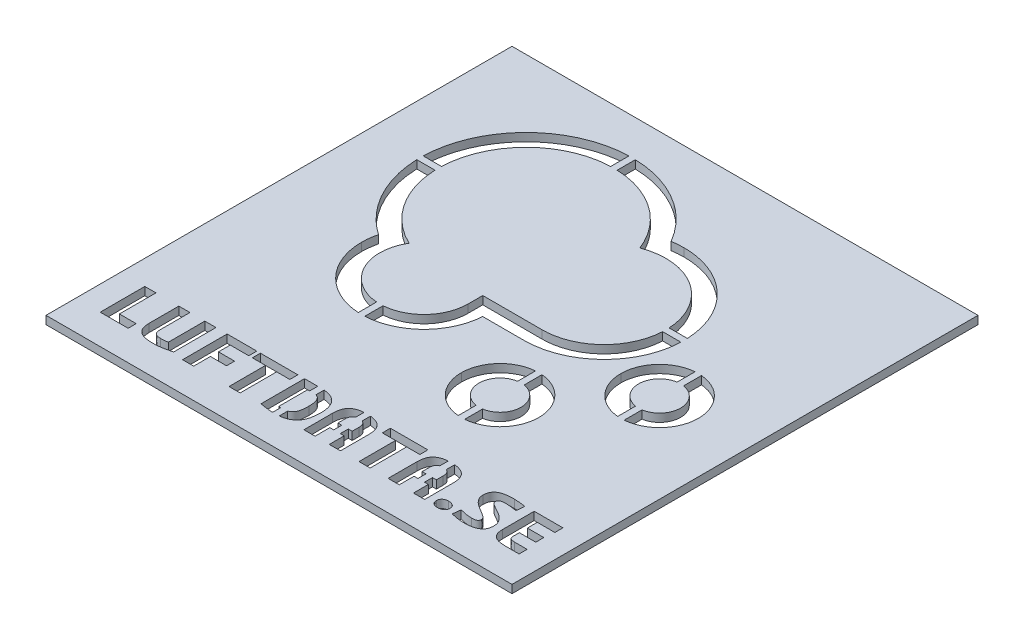
SolidWorks part; units mm, degrees
ref_plane "Front Plane" through (0, 0, 0) normal (0, 0, 1) x (1, 0, 0)
ref_plane "Top Plane" through (0, 0, 0) normal (0, 1, 0) x (1, 0, 0)
ref_plane "Right Plane" through (0, 0, 0) normal (1, 0, 0) x (0, 0, -1)
sketch "Logo" plane through (0, 0, 0) normal (0, 1, 0) x (1, 0, 0)
  line L0 (6.8222, -9.5648) -> (-7.8428, -9.5648)
  line L1 (-7.8428, -9.5648) -> (-7.8428, -13.1554)
  line L2 (-3.3693, -14.065) -> (6.822, -14.0654)
  line L4 (-45.0278, 38.3096) -> (45.0278, 38.3096) construction
  line L5 (-45.0278, 38.3096) -> (-45.0278, -38.3096) construction
  line L6 (-45.0278, -38.3096) -> (45.0278, -38.3096) construction
  line L7 (45.0278, 38.3096) -> (45.0278, -38.3096) construction
  spline S0 degree 3 poles (-18.8378, 33.8102) (-9.6328, 33.8102) (-1.7677, 28.0702) (1.3772, 19.9802) knots 0 0 0 0 1 1 1 1
  spline S1 degree 3 poles (1.3772, 19.9802) (3.0672, 20.6252) (4.9022, 20.9802) (6.8222, 20.9802) knots 1 1 1 1 2 2 2 2
  spline S2 degree 3 poles (6.8222, 20.9802) (15.2572, 20.9802) (22.0922, 14.1452) (22.0922, 5.7102) knots 2 2 2 2 3 3 3 3
  spline S3 degree 3 poles (22.0922, 5.7102) (22.0922, -2.7248) (15.2572, -9.5648) (6.8222, -9.5648) knots 3 3 3 3 4 4 4 4
  spline S4 degree 3 poles (-7.8428, -13.1554) (-7.8429, -19.1854) (-12.7331, -24.0753) (-18.7631, -24.0751) knots 6 6 6 6 7 7 7 7
  spline S5 degree 3 poles (-18.7631, -24.0751) (-24.7931, -24.0749) (-29.6829, -19.1848) (-29.6828, -13.1548) knots 7 7 7 7 8 8 8 8
  spline S6 degree 3 poles (-29.6828, -13.1548) (-29.6828, -11.0798) (-29.1028, -9.1398) (-28.0978, -7.4898) knots 8 8 8 8 9 9 9 9
  spline S7 degree 3 poles (-28.0978, -7.4898) (-35.4478, -4.0198) (-40.5278, 3.4602) (-40.5278, 12.1252) knots 9 9 9 9 10 10 10 10
  spline S8 degree 3 poles (-40.5278, 12.1252) (-40.5278, 24.1002) (-30.8178, 33.8102) (-18.8378, 33.8102) knots 10 10 10 10 11 11 11 11
  spline S9 degree 3 poles (-18.8378, 38.3096) (-33.279, 38.3096) (-45.0278, 26.5631) (-45.0278, 12.1246) knots 0 0 0 0 1 1 1 1
  spline S10 degree 3 poles (-45.0278, 12.1246) (-45.0278, 3.4834) (-40.7005, -4.5805) (-33.7243, -9.4193) knots 1 1 1 1 2 2 2 2
  spline S11 degree 3 poles (-33.7243, -9.4193) (-34.0275, -10.6346) (-34.1828, -11.8887) (-34.1828, -13.1554) knots 2 2 2 2 3 3 3 3
  spline S12 degree 3 poles (-34.1828, -13.1554) (-34.1828, -21.658) (-27.2654, -28.5754) (-18.7628, -28.5754) knots 3 3 3 3 4 4 4 4
  spline S13 degree 3 poles (-18.7628, -28.5754) (-10.5653, -28.5754) (-3.8414, -22.1461) (-3.3693, -14.065) knots 4 4 4 4 5 5 5 5
  spline S14 degree 3 poles (6.822, -14.0654) (17.7234, -14.0654) (26.5922, -5.1944) (26.5922, 5.7096) knots 6 6 6 6 7 7 7 7
  spline S15 degree 3 poles (26.5922, 5.7096) (26.5922, 16.6108) (17.7234, 25.4796) (6.8222, 25.4796) knots 7 7 7 7 8 8 8 8
  spline S16 degree 3 poles (6.8222, 25.4796) (5.8114, 25.4796) (4.8099, 25.4039) (3.8223, 25.2532) knots 8 8 8 8 9 9 9 9
  spline S17 degree 3 poles (3.8223, 25.2532) (1.9103, 28.5555) (-0.7065, 31.4051) (-3.8848, 33.6202) knots 9 9 9 9 10 10 10 10
  spline S18 degree 3 poles (-3.8848, 33.6202) (-8.2867, 36.688) (-13.4573, 38.3096) (-18.8378, 38.3096) knots 10 10 10 10 11 11 11 11
  spline S19 degree 3 poles (35.4472, -14.399) (32.584, -14.399) (30.2628, -12.0779) (30.2628, -9.2146) (30.2628, -6.3513) (32.584, -4.0302) (35.4472, -4.0302) knots 2 2 2 2 3 3 3 4 4 4 4
  spline S20 degree 3 poles (35.4472, -4.0302) (38.3105, -4.0302) (40.6316, -6.3513) (40.6316, -9.2146) (40.6316, -12.0779) (38.3105, -14.399) (35.4472, -14.399) knots 0 0 0 0 1 1 1 2 2 2 2
  spline S21 degree 3 poles (35.4472, 0.3545) (30.1708, 0.3545) (25.8782, -3.9382) (25.8782, -9.2146) knots 0 0 0 0 1 1 1 1
  spline S22 degree 3 poles (25.8782, -9.2146) (25.8782, -14.491) (30.1708, -18.7837) (35.4472, -18.7837) knots 1 1 1 1 2 2 2 2
  spline S23 degree 3 poles (35.4472, -18.7837) (40.7236, -18.7837) (45.0163, -14.491) (45.0163, -9.2146) knots 2 2 2 2 3 3 3 3
  spline S24 degree 3 poles (45.0163, -9.2146) (45.0163, -3.9382) (40.7236, 0.3545) (35.4472, 0.3545) knots 3 3 3 3 4 4 4 4
  spline S25 degree 3 poles (15.5836, -33.9035) (12.7203, -33.9035) (10.3992, -31.5824) (10.3992, -28.7191) (10.3992, -25.8559) (12.7203, -23.5347) (15.5836, -23.5347) knots 2 2 2 2 3 3 3 4 4 4 4
  spline S26 degree 3 poles (15.5836, -23.5347) (18.4468, -23.5347) (20.768, -25.8559) (20.768, -28.7191) (20.768, -31.5824) (18.4468, -33.9035) (15.5836, -33.9035) knots 0 0 0 0 1 1 1 2 2 2 2
  spline S27 degree 3 poles (15.5836, -19.1501) (10.3072, -19.1501) (6.0145, -23.4427) (6.0145, -28.7191) knots 0 0 0 0 1 1 1 1
  spline S28 degree 3 poles (6.0145, -28.7191) (6.0145, -33.9955) (10.3072, -38.2882) (15.5836, -38.2882) knots 1 1 1 1 2 2 2 2
  spline S29 degree 3 poles (15.5836, -38.2882) (20.86, -38.2882) (25.1526, -33.9955) (25.1526, -28.7191) knots 2 2 2 2 3 3 3 3
  spline S30 degree 3 poles (25.1526, -28.7191) (25.1526, -23.4427) (20.86, -19.1501) (15.5836, -19.1501) knots 3 3 3 3 4 4 4 4
  point P39 (0, 0)
  point P40 (45.0278, 0)
  point P41 (0, 38.3096)
sketch "Sketch4" plane through (0, 0, 0) normal (0, 1, 0) x (1, 0, 0)
  line L0 (-7.8428, -9.5648) -> (-7.8428, -13.1554) construction
  line L1 (-3.3693, -14.065) -> (6.822, -14.0654) construction
  line L2 (6.8222, -9.5648) -> (-7.8428, -9.5648) construction
  line L3 (-7.8428, -9.5648) -> (-7.8428, -13.1554)
  line L4 (-3.3693, -14.065) -> (6.822, -14.0654)
  line L5 (6.8222, -9.5648) -> (-7.8428, -9.5648)
  line L6 (-45.0278, 38.3096) -> (45.0278, 38.3096) construction
  line L7 (-57.5, 47.3096) -> (57.5, 47.3096)
  line L8 (-57.5, 47.3096) -> (-57.5, -67.6904)
  line L9 (-57.5, -67.6904) -> (57.5, -67.6904)
  line L10 (57.5, 47.3096) -> (57.5, -67.6904)
  line L11 (-57.5, -60.3243) -> (57.5, -60.3243) construction
  spline S0 degree 3 poles (-1563.1181, 2507.2411) (296.2295, -25.5053) (10.3992, -60.4928) (10.3992, -28.7191) (10.3992, 3.0546) (296.2339, -31.9301) (-1563.1617, -2564.7905) knots -8.096964 -8.096964 -8.096964 -8.096964 3 3 3 14.09705 14.09705 14.09705 14.09705 only from (15.5836, -33.9035) to (15.5836, -23.5347) construction
  spline S1 degree 3 poles (1594.2613, -2564.7108) (-265.0604, -31.9294) (20.768, 3.0543) (20.768, -28.7191) (20.768, -60.4931) (-265.0683, -25.5045) (1594.3389, 2507.3265) knots -10.096934 -10.096934 -10.096934 -10.096934 1 1 1 12.097089 12.097089 12.097089 12.097089 only from (15.5836, -23.5347) to (15.5836, -33.9035) construction
  spline S2 degree 3 poles (1460.132, 2576.6875) (-1926.2736, -2375.5534) (2362.3929, 1913.1024) (-2589.7209, -1473.1977) knots -6.113417 -6.113417 -6.113417 -6.113417 11.113298 11.113298 11.113298 11.113298 only from (15.5836, -38.2882) to (25.1526, -28.7191) construction
  spline S3 degree 3 poles (2620.9856, -1473.2612) (-2331.2474, 1913.1308) (1957.403, -2375.5206) (-1428.8942, 2576.577) knots -7.113406 -7.113406 -7.113406 -7.113406 10.113288 10.113288 10.113288 10.113288 only from (6.0145, -28.7191) to (15.5836, -38.2882) construction
  spline S4 degree 3 poles (-1428.9697, -2634.1257) (1957.4456, 2318.1152) (-2331.2307, -1970.5406) (2620.8928, 1415.7595) knots -8.113417 -8.113417 -8.113417 -8.113417 9.113298 9.113298 9.113298 9.113298 only from (15.5836, -19.1501) to (6.0145, -28.7191) construction
  spline S5 degree 3 poles (-2589.823, 1415.8293) (2362.4179, -1970.5763) (-1926.2379, 2318.0902) (1460.0622, -2634.0236) knots -5.113417 -5.113417 -5.113417 -5.113417 12.113298 12.113298 12.113298 12.113298 only from (25.1526, -28.7191) to (15.5836, -19.1501) construction
  spline S6 degree 3 poles (2640.8538, -1453.7631) (-2311.3871, 1932.6426) (1977.2687, -2356.024) (-1409.0314, 2596.0899) knots -7.113417 -7.113417 -7.113417 -7.113417 10.113298 10.113298 10.113298 10.113298 only from (25.8782, -9.2146) to (35.4472, -18.7837) construction
  spline S7 degree 3 poles (-1543.2917, 2526.7312) (316.0935, -6.0009) (30.2628, -40.9882) (30.2628, -9.2146) (30.2628, 22.5593) (316.0981, -12.4284) (-1543.337, -2545.2311) knots -8.096943 -8.096943 -8.096943 -8.096943 3 3 3 14.097033 14.097033 14.097033 14.097033 only from (35.4472, -14.399) to (35.4472, -4.0302) construction
  spline S8 degree 3 poles (1614.1399, -2545.1838) (-245.1982, -12.428) (40.6316, 22.5591) (40.6316, -9.2146) (40.6316, -40.9885) (-245.2027, -6.0002) (1614.1834, 2526.805) knots -10.096964 -10.096964 -10.096964 -10.096964 1 1 1 12.09705 12.09705 12.09705 12.09705 only from (35.4472, -4.0302) to (35.4472, -14.399) construction
  spline S9 degree 3 poles (1479.9957, 2596.192) (-1906.41, -2356.0489) (2382.2566, 1932.6069) (-2569.8572, -1453.6932) knots -6.113417 -6.113417 -6.113417 -6.113417 11.113298 11.113298 11.113298 11.113298 only from (35.4472, -18.7837) to (45.0163, -9.2146) construction
  spline S10 degree 3 poles (-2569.9594, 1435.3387) (2382.2815, -1951.0767) (-1906.3743, 2337.5997) (1479.9259, -2614.5239) knots -5.113417 -5.113417 -5.113417 -5.113417 12.113298 12.113298 12.113298 12.113298 only from (45.0163, -9.2146) to (35.4472, 0.3545) construction
  spline S11 degree 3 poles (-1409.0948, -2614.6166) (1977.2971, 2337.6164) (-2311.3542, -1951.034) (2640.7433, 1435.2632) knots -8.113406 -8.113406 -8.113406 -8.113406 9.113288 9.113288 9.113288 9.113288 only from (35.4472, 0.3545) to (25.8782, -9.2146) construction
  spline S12 degree 3 poles (2687.9195, 1203.4807) (-2446.2841, -1870.2517) (1861.9201, 2440.7726) (-1208.2564, -2695.4033) knots 3.937482 3.937482 3.937482 3.937482 17.062235 17.062235 17.062235 17.062235 only from (-40.5278, 12.1252) to (-18.8378, 33.8102) construction
  spline S13 degree 3 poles (-1146.2521, -2713.887) (1850.0041, 2462.8367) (-2469.9297, -1856.203) (2707.2807, 1139.0758) knots -5.645374 -5.645374 -5.645374 -5.645374 6.645042 6.645042 6.645042 6.645042 only from (-18.8378, 38.3096) to (-45.0278, 12.1246) construction
  spline S14 degree 3 poles (2391.1864, -1692.7249) (-2002.7517, 2377.3435) (1274.203, -2791.9559) (-532.9439, 2921.2731) knots -8.245789 -8.245789 -8.245789 -8.245789 11.415145 11.415145 11.415145 11.415145 only from (-45.0278, 12.1246) to (-33.7243, -9.4193) construction
  spline S15 degree 3 poles (-1203.0444, 2726.4883) (1857.5978, -2422.8591) (-2442.9291, 1900.2261) (2685.5379, -1184.1756) knots 0.236451 0.236451 0.236451 0.236451 18.38266 18.38266 18.38266 18.38266 only from (-28.0978, -7.4898) to (-40.5278, 12.1252) construction
  spline S16 degree 3 poles (2602.1303, 1397.6362) (-2378.1491, -1949.1531) (1918.6495, 2348.8318) (-1435.6923, -2640.3784) knots -14.455557 -14.455557 -14.455557 -14.455557 33.350301 33.350301 33.350301 33.350301 only from (-29.6828, -13.1548) to (-28.0978, -7.4898) construction
  spline S17 degree 3 poles (214.4881, -2977.5634) (449.8224, 3000.5485) (-1185.1093, -2829.6682) (1722.3591, 2392.541) knots -45.752091 -45.752091 -45.752091 -45.752091 49.547523 49.547523 49.547523 49.547523 only from (-33.7243, -9.4193) to (-34.1828, -13.1554) construction
  spline S18 degree 3 poles (2644.7906, -1323.6407) (-2409.7939, 1897.8056) (1892.1649, -2404.1834) (-1329.1976, 2650.3473) knots -3.84167 -3.84167 -3.84167 -3.84167 10.84161 10.84161 10.84161 10.84161 only from (-34.1828, -13.1554) to (-18.7628, -28.5754) construction
  spline S19 degree 3 poles (-1423.9537, 2610.6341) (1912.8518, -2371.6713) (-2377.1155, 1918.631) (2604.8722, -1418.524) knots -0.758808 -0.758808 -0.758808 -0.758808 15.758776 15.758776 15.758776 15.758776 only from (-18.7631, -24.0751) to (-29.6828, -13.1548) construction
  spline S20 degree 3 poles (-2642.5299, -1418.3835) (2339.7195, 1918.4855) (-1950.5068, -2371.5174) (1386.5613, 2610.4702) knots -1.758788 -1.758788 -1.758788 -1.758788 14.758714 14.758714 14.758714 14.758714 only from (-7.8428, -13.1554) to (-18.7631, -24.0751) construction
  spline S21 degree 3 poles (1291.8934, 2650.2912) (-1929.9587, -2404.068) (2372.5701, 1897.6329) (-2682.6404, -1323.4175) knots -3.096668 -3.096668 -3.096668 -3.096668 12.133918 12.133918 12.133918 12.133918 only from (-18.7628, -28.5754) to (-3.3693, -14.065) construction
  spline S22 degree 3 poles (1235.9369, 2699.4183) (-1885.1295, -2412.1699) (2424.1402, 1898.3378) (-2686.577, -1224.0265) knots -0.253933 -0.253933 -0.253933 -0.253933 13.254292 13.254292 13.254292 13.254292 only from (6.822, -14.0654) to (26.5922, 5.7096) construction
  spline S23 degree 3 poles (-2657.0297, -1304.1441) (2395.1026, 1916.7716) (-1899.6373, -2386.2468) (1311.6988, 2671.9485) knots -3.883603 -3.883603 -3.883603 -3.883603 10.882064 10.882064 10.882064 10.882064 only from (22.0922, 5.7102) to (6.8222, -9.5648) construction
  spline S24 degree 3 poles (1313.6625, -2659.6639) (-1901.6986, 2395.875) (2396.9632, -1902.8095) (-2658.4961, 1312.5371) knots -4.885072 -4.885072 -4.885072 -4.885072 9.885031 9.885031 9.885031 9.885031 only from (6.8222, 20.9802) to (22.0922, 5.7102) construction
  spline S25 degree 3 poles (2616.089, 1453.3855) (-2310.1363, -2015.9175) (1831.1355, 2474.405) (-1214.6176, -2700.559) knots -32.679312 -32.679312 -32.679312 -32.679312 32.027034 32.027034 32.027034 32.027034 only from (1.3772, 19.9802) to (6.8222, 20.9802) construction
  spline S26 degree 3 poles (-2120.1619, -2019.1293) (2659.5519, 1065.2455) (-2852.9999, 43.9931) (2729.2966, -1106.8439) knots -75.028946 -75.028946 -75.028946 -75.028946 93.179941 93.179941 93.179941 93.179941 only from (6.8222, 25.4796) to (3.8223, 25.2532) construction
  spline S27 degree 3 poles (-2686.7092, 1235.1871) (2424.4098, -1886.5908) (-1885.492, 2423.2889) (1236.3167, -2687.8204) knots 0.745633 0.745633 0.745633 0.745633 14.254374 14.254374 14.254374 14.254374 only from (26.5922, 5.7096) to (6.8222, 25.4796) construction
  spline S28 degree 3 poles (-2686.4652, 1266.0216) (2203.0185, -2039.9601) (-1492.4842, 2651.6057) (567.9184, -2873.2867) knots -13.877405 -13.877405 -13.877405 -13.877405 32.557755 32.557755 32.557755 32.557755 only from (3.8223, 25.2532) to (-3.8848, 33.6202) construction
  spline S29 degree 3 poles (-2914.0606, -511.8571) (2955.6046, -405.3584) (-2699.1603, 1366.4164) (2055.3883, -2073.9653) knots -6.478561 -6.478561 -6.478561 -6.478561 27.50147 27.50147 27.50147 27.50147 only from (-3.8848, 33.6202) to (-18.8378, 38.3096) construction
  spline S30 degree 3 poles (1169.0079, -2696.1689) (-1898.0758, 2443.8133) (2408.0009, -1875.2213) (-2726.461, 1209.6782) knots -7.88221 -7.88221 -7.88221 -7.88221 9.188291 9.188291 9.188291 9.188291 only from (-18.8378, 33.8102) to (1.3772, 19.9802) construction
  spline S31 degree 3 poles (15.5836, -33.9035) (12.7203, -33.9035) (10.3992, -31.5824) (10.3992, -28.7191) (10.3992, -25.8559) (12.7203, -23.5347) (15.5836, -23.5347) knots 2 2 2 2 3 3 3 4 4 4 4
  spline S32 degree 3 poles (15.5836, -23.5347) (18.4468, -23.5347) (20.768, -25.8559) (20.768, -28.7191) (20.768, -31.5824) (18.4468, -33.9035) (15.5836, -33.9035) knots 0 0 0 0 1 1 1 2 2 2 2
  spline S33 degree 3 poles (15.5836, -38.2882) (20.86, -38.2882) (25.1526, -33.9955) (25.1526, -28.7191) knots 2 2 2 2 3 3 3 3
  spline S34 degree 3 poles (6.0145, -28.7191) (6.0145, -33.9955) (10.3072, -38.2882) (15.5836, -38.2882) knots 1 1 1 1 2 2 2 2
  spline S35 degree 3 poles (15.5836, -19.1501) (10.3072, -19.1501) (6.0145, -23.4427) (6.0145, -28.7191) knots 0 0 0 0 1 1 1 1
  spline S36 degree 3 poles (25.1526, -28.7191) (25.1526, -23.4427) (20.86, -19.1501) (15.5836, -19.1501) knots 3 3 3 3 4 4 4 4
  spline S37 degree 3 poles (25.8782, -9.2146) (25.8782, -14.491) (30.1708, -18.7837) (35.4472, -18.7837) knots 1 1 1 1 2 2 2 2
  spline S38 degree 3 poles (35.4472, -14.399) (32.584, -14.399) (30.2628, -12.0779) (30.2628, -9.2146) (30.2628, -6.3513) (32.584, -4.0302) (35.4472, -4.0302) knots 2 2 2 2 3 3 3 4 4 4 4
  spline S39 degree 3 poles (35.4472, -4.0302) (38.3105, -4.0302) (40.6316, -6.3513) (40.6316, -9.2146) (40.6316, -12.0779) (38.3105, -14.399) (35.4472, -14.399) knots 0 0 0 0 1 1 1 2 2 2 2
  spline S40 degree 3 poles (35.4472, -18.7837) (40.7236, -18.7837) (45.0163, -14.491) (45.0163, -9.2146) knots 2 2 2 2 3 3 3 3
  spline S41 degree 3 poles (45.0163, -9.2146) (45.0163, -3.9382) (40.7236, 0.3545) (35.4472, 0.3545) knots 3 3 3 3 4 4 4 4
  spline S42 degree 3 poles (35.4472, 0.3545) (30.1708, 0.3545) (25.8782, -3.9382) (25.8782, -9.2146) knots 0 0 0 0 1 1 1 1
  spline S43 degree 3 poles (-40.5278, 12.1252) (-40.5278, 24.1002) (-30.8178, 33.8102) (-18.8378, 33.8102) knots 10 10 10 10 11 11 11 11
  spline S44 degree 3 poles (-18.8378, 38.3096) (-33.279, 38.3096) (-45.0278, 26.5631) (-45.0278, 12.1246) knots 0 0 0 0 1 1 1 1
  spline S45 degree 3 poles (-45.0278, 12.1246) (-45.0278, 3.4834) (-40.7005, -4.5805) (-33.7243, -9.4193) knots 1 1 1 1 2 2 2 2
  spline S46 degree 3 poles (-28.0978, -7.4898) (-35.4478, -4.0198) (-40.5278, 3.4602) (-40.5278, 12.1252) knots 9 9 9 9 10 10 10 10
  spline S47 degree 3 poles (-29.6828, -13.1548) (-29.6828, -11.0798) (-29.1028, -9.1398) (-28.0978, -7.4898) knots 8 8 8 8 9 9 9 9
  spline S48 degree 3 poles (-33.7243, -9.4193) (-34.0275, -10.6346) (-34.1828, -11.8887) (-34.1828, -13.1554) knots 2 2 2 2 3 3 3 3
  spline S49 degree 3 poles (-34.1828, -13.1554) (-34.1828, -21.658) (-27.2654, -28.5754) (-18.7628, -28.5754) knots 3 3 3 3 4 4 4 4
  spline S50 degree 3 poles (-18.7631, -24.0751) (-24.7931, -24.0749) (-29.6829, -19.1848) (-29.6828, -13.1548) knots 7 7 7 7 8 8 8 8
  spline S51 degree 3 poles (-7.8428, -13.1554) (-7.8429, -19.1854) (-12.7331, -24.0753) (-18.7631, -24.0751) knots 6 6 6 6 7 7 7 7
  spline S52 degree 3 poles (-18.7628, -28.5754) (-10.5653, -28.5754) (-3.8414, -22.1461) (-3.3693, -14.065) knots 4 4 4 4 5 5 5 5
  spline S53 degree 3 poles (6.822, -14.0654) (17.7234, -14.0654) (26.5922, -5.1944) (26.5922, 5.7096) knots 6 6 6 6 7 7 7 7
  spline S54 degree 3 poles (22.0922, 5.7102) (22.0922, -2.7248) (15.2572, -9.5648) (6.8222, -9.5648) knots 3 3 3 3 4 4 4 4
  spline S55 degree 3 poles (6.8222, 20.9802) (15.2572, 20.9802) (22.0922, 14.1452) (22.0922, 5.7102) knots 2 2 2 2 3 3 3 3
  spline S56 degree 3 poles (1.3772, 19.9802) (3.0672, 20.6252) (4.9022, 20.9802) (6.8222, 20.9802) knots 1 1 1 1 2 2 2 2
  spline S57 degree 3 poles (6.8222, 25.4796) (5.8114, 25.4796) (4.8099, 25.4039) (3.8223, 25.2532) knots 8 8 8 8 9 9 9 9
  spline S58 degree 3 poles (26.5922, 5.7096) (26.5922, 16.6108) (17.7234, 25.4796) (6.8222, 25.4796) knots 7 7 7 7 8 8 8 8
  spline S59 degree 3 poles (3.8223, 25.2532) (1.9103, 28.5555) (-0.7065, 31.4051) (-3.8848, 33.6202) knots 9 9 9 9 10 10 10 10
  spline S60 degree 3 poles (-3.8848, 33.6202) (-8.2867, 36.688) (-13.4573, 38.3096) (-18.8378, 38.3096) knots 10 10 10 10 11 11 11 11
  spline S61 degree 3 poles (-18.8378, 33.8102) (-9.6328, 33.8102) (-1.7677, 28.0702) (1.3772, 19.9802) knots 0 0 0 0 1 1 1 1
  text T0 "LUFTDATA.SE" font "3ds" height 11
  point P10 (0, 47.3096)
  point P20 (0, 0)
  dimension "D1" = 115
  dimension "D2" = 115
  dimension "D3" = 9
extrude "Boss-Extrude2" add sketch "Sketch4" along normal blind 2 contours L8 L11 L10 L7 S60 S59 S57 S58 S53 L4 S52 S49 S48 S45 S44 S42 S41 S40 S37 S36 S33 S34 S35 | L11 L8 L9 L10 | S61 S43 S46 S47 S50 S51 L3 L5 S54 S55 S56 | S32 S31 | S39 S38
sketch "Sketch5" plane through (0, 2, 0) normal (0, 1, 0) x (1, 0, 0)
  text T0 "LUFTDATA.SE" font "3ds" height 11
extrude "Cut-Extrude1" cut sketch "Sketch5" against normal up to next (2 mm away)
sketch "Sketch6" plane through (0, 2, 0) normal (0, 1, 0) x (1, 0, 0)
  line L0 (5.0417, -56.6576) -> (1.5278, -56.6576) construction
  line L1 (-19.6378, 31.1469) -> (-18.0378, 31.1469)
  line L2 (-19.6378, 31.1469) -> (-19.6378, 40.1633)
  line L3 (-19.6378, 40.1633) -> (-18.0378, 40.1633)
  line L4 (-18.0378, 31.1469) -> (-18.0378, 40.1633)
  line L5 (-19.6378, 31.1469) -> (-18.0378, 40.1633) construction
  line L6 (-19.6378, 40.1633) -> (-18.0378, 31.1469) construction
  line L7 (-48.9036, 12.9246) -> (-36.3551, 12.9246)
  line L8 (-48.9036, 12.9246) -> (-48.9036, 11.3246)
  line L9 (-48.9036, 11.3246) -> (-36.3551, 11.3246)
  line L10 (-36.3551, 12.9246) -> (-36.3551, 11.3246)
  line L11 (-48.9036, 12.9246) -> (-36.3551, 11.3246) construction
  line L12 (-48.9036, 11.3246) -> (-36.3551, 12.9246) construction
  line L13 (20.6999, 6.5102) -> (28.6008, 6.5102)
  line L14 (20.6999, 6.5102) -> (20.6999, 4.9102)
  line L15 (20.6999, 4.9102) -> (28.6008, 4.9102)
  line L16 (28.6008, 6.5102) -> (28.6008, 4.9102)
  line L17 (20.6999, 6.5102) -> (28.6008, 4.9102) construction
  line L18 (20.6999, 4.9102) -> (28.6008, 6.5102) construction
  line L19 (-19.5631, -31.8281) -> (-17.9631, -31.8281)
  line L20 (-19.5631, -31.8281) -> (-19.5631, -20.9935)
  line L21 (-19.5631, -20.9935) -> (-17.9631, -20.9935)
  line L22 (-17.9631, -31.8281) -> (-17.9631, -20.9935)
  line L23 (-19.5631, -31.8281) -> (-17.9631, -20.9935) construction
  line L24 (-19.5631, -20.9935) -> (-17.9631, -31.8281) construction
  line L25 (34.6472, -21.0813) -> (36.2472, -21.0813)
  line L26 (34.6472, -21.0813) -> (34.6472, 2.6569)
  line L27 (34.6472, 2.6569) -> (36.2472, 2.6569)
  line L28 (36.2472, -21.0813) -> (36.2472, 2.6569)
  line L29 (34.6472, -21.0813) -> (36.2472, 2.6569) construction
  line L30 (34.6472, 2.6569) -> (36.2472, -21.0813) construction
  line L31 (14.7836, -40.0383) -> (16.3836, -40.0383)
  line L32 (14.7836, -40.0383) -> (14.7836, -16.2942)
  line L33 (14.7836, -16.2942) -> (16.3836, -16.2942)
  line L34 (16.3836, -40.0383) -> (16.3836, -16.2942)
  line L35 (14.7836, -40.0383) -> (16.3836, -16.2942) construction
  line L36 (14.7836, -16.2942) -> (16.3836, -40.0383) construction
  line L37 (-8.8124, -52.7155) -> (-7.2124, -52.7155)
  line L38 (-8.8124, -52.7155) -> (-8.8124, -47.9868)
  line L39 (-8.8124, -47.9868) -> (-7.2124, -47.9868)
  line L40 (-7.2124, -52.7155) -> (-7.2124, -47.9868)
  line L41 (-8.8124, -52.7155) -> (-7.2124, -47.9868) construction
  line L42 (-8.8124, -47.9868) -> (-7.2124, -52.7155) construction
  line L43 (-8.8124, -54.1347) -> (-7.2124, -54.1347)
  line L44 (-8.8124, -54.1347) -> (-8.8124, -61.6722)
  line L45 (-8.8124, -61.6722) -> (-7.2124, -61.6722)
  line L46 (-7.2124, -54.1347) -> (-7.2124, -61.6722)
  line L47 (-8.8124, -54.1347) -> (-7.2124, -61.6722) construction
  line L48 (-8.8124, -61.6722) -> (-7.2124, -54.1347) construction
  line L49 (2.4847, -47.4545) -> (4.0847, -47.4545)
  line L50 (2.4847, -47.4545) -> (2.4847, -58.3256)
  line L51 (2.4847, -58.3256) -> (4.0847, -58.3256)
  line L52 (4.0847, -47.4545) -> (4.0847, -58.3256)
  line L53 (23.2625, -47.4545) -> (24.8625, -47.4545)
  line L54 (23.2625, -47.4545) -> (23.2625, -58.3256)
  line L55 (23.2625, -58.3256) -> (24.8625, -58.3256)
  line L56 (24.8625, -47.4545) -> (24.8625, -58.3256)
  line L57 (25.8194, -56.6576) -> (22.3056, -56.6576) construction
  point P0 (-18.8378, 35.6551)
  point P5 (24.6504, 5.7102)
  point P7 (-42.6293, 12.1246)
  point P16 (-18.7631, -26.4108)
  point P21 (35.4472, -9.2122)
  point P26 (15.5836, -28.1663)
  point P31 (-8.0124, -50.3512)
  point P36 (-8.0124, -57.9034)
  point P49 (0, 0)
  point P51 (0, 0)
  point P53 (0, 0)
  point P55 (0, 0)
  point P57 (0, 0)
  point P59 (3.2847, -47.4545)
  point P62 (3.2847, -56.6576)
  point P63 (24.0625, -58.3256)
  point P66 (24.0625, -56.6576)
  point P67 (0, 0)
  dimension "D1" = 1.6
extrude "Boss-Extrude3" add sketch "Sketch6" against normal through all
